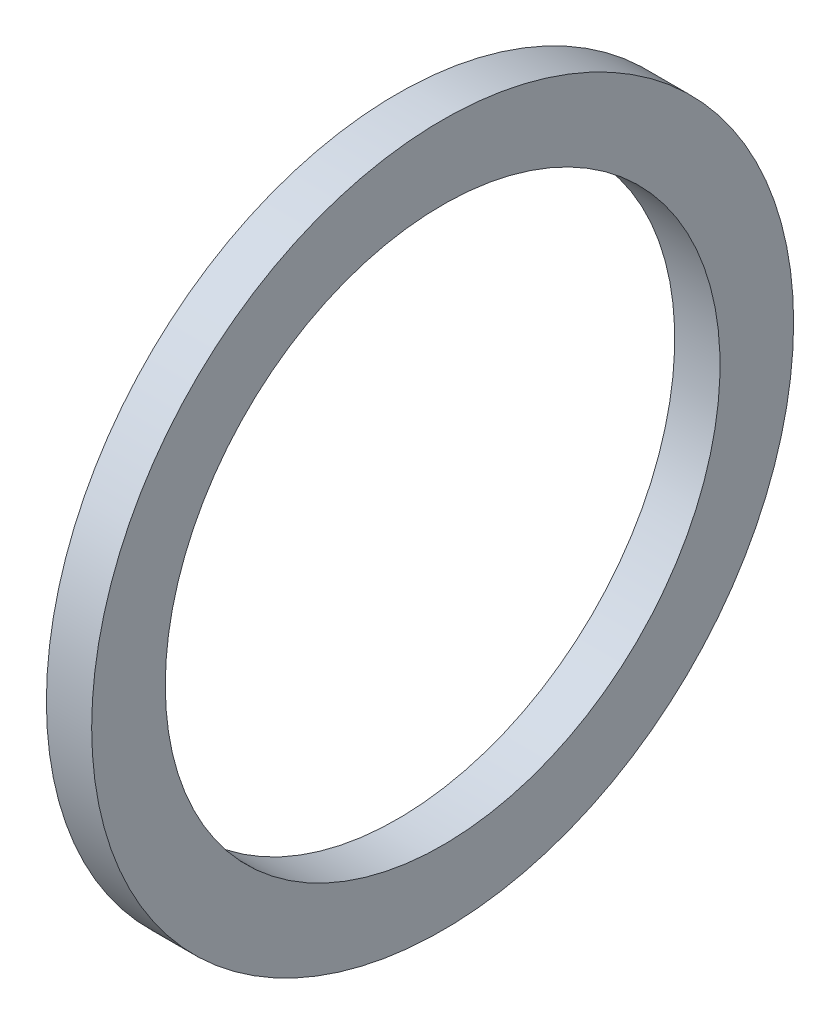
SolidWorks part; units mm, degrees
ref_plane "Front Plane" through (0, 0, 0) normal (0, 0, 1) x (1, 0, 0)
ref_plane "Top Plane" through (0, 0, 0) normal (0, 1, 0) x (1, 0, 0)
ref_plane "Right Plane" through (0, 0, 0) normal (1, 0, 0) x (0, 0, -1)
sketch "Sketch1" plane through (0, 0, 0) normal (0, 0, 1) x (1, 0, 0)
  line L0 (-43.7166, 0) -> (79.6876, 0) construction
  line L2 (0, -12.446) -> (2.032, -12.446)
  line L3 (0, -12.446) -> (0, -15.748)
  line L4 (0, -15.748) -> (2.032, -15.748)
  line L5 (2.032, -12.446) -> (2.032, -15.748)
  dimension "A" = 24.892
  dimension "B" = 31.496
  dimension "C" = 2.032
revolve "Revolve1" add sketch "Sketch1" angle 360 about L0
sketch "Sketch2" [suppressed] plane through (0, 0, 0) normal (0, 0, 1) x (1, 0, 0)
  line L0 (-34.685, 0) -> (47.6686, 0) construction
  circle A0 centre (2.54, -5.715) radius 0.762
  dimension "D1" = 2.54
  dimension "E" = 2.032
  dimension "D" = 22.098
revolve "Revolve3" [suppressed] add sketch "Sketch2" angle 360 about L0
